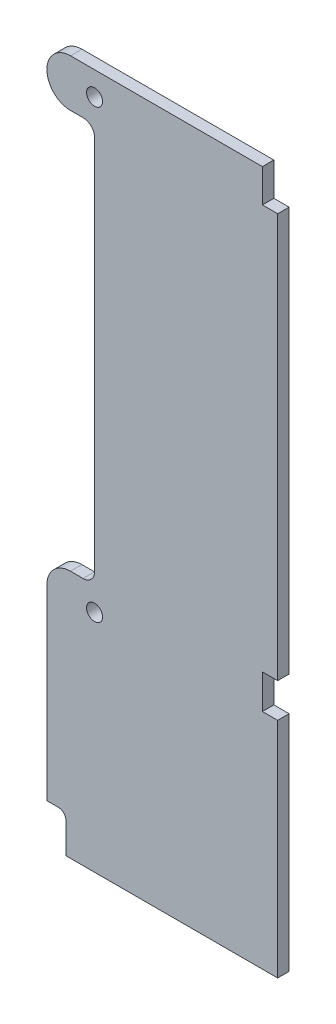
SolidWorks part; units mm, degrees
material "6061-T6 Black anodised"
ref_plane "Front Plane" through (0, 0, 0) normal (0, 0, 1) x (1, 0, 0)
ref_plane "Top Plane" through (0, 0, 0) normal (0, 1, 0) x (1, 0, 0)
ref_plane "Right Plane" through (0, 0, 0) normal (1, 0, 0) x (0, 0, -1)
sketch "Sketch1" plane through (0, 0, 0) normal (0, 0, 1) x (1, 0, 0)
  line L0 (-6.3, 110.8) -> (-3, 110.8)
  line L1 (-6.3, 123.2) -> (44, 123.2)
  line L2 (-12.5, 0) -> (-12.5, -49)
  line L3 (-7.5, -59) -> (48, -59)
  line L4 (-12.5, -49) -> (-9.5, -49)
  line L5 (0, 107.8) -> (0, 9.2)
  line L6 (-3, 6.2) -> (-6.3, 6.2)
  line L7 (48, -0.5) -> (44, -0.5)
  line L8 (44, -0.5) -> (44, 8.5)
  line L9 (44, 8.5) -> (48, 8.5)
  line L10 (48, 114.5) -> (44, 114.5)
  line L11 (44, 114.5) -> (44, 123.2)
  line L12 (-7.5, -51) -> (-7.5, -59)
  line L13 (48, 114.5) -> (48, 8.5)
  line L14 (48, -0.5) -> (48, -59)
  circle A0 centre (0, 0) radius 2.1
  circle A1 centre (0, 117) radius 2.1
  arc A2 (-7.5, -51) -> (-9.5, -49) centre (-9.5, -51) ccw
  arc A3 (-6.3, 6.2) -> (-12.5, 0) centre (-6.3, 0) ccw
  arc A4 (0, 107.8) -> (-3, 110.8) centre (-3, 107.8) ccw
  arc A5 (0, 9.2) -> (-3, 6.2) centre (-3, 9.2) cw
  arc A6 (-6.3, 123.2) -> (-6.3, 110.8) centre (-6.3, 117) ccw
  point P10 (-12.5, 117)
  point P27 (44, 4)
  dimension "D6" = 4.2
  dimension "D8" = 3
  dimension "D15" = 2
  dimension "D1" = 12.5
  dimension "D2" = 117
  dimension "D3" = 59
  dimension "D4" = 182.2
  dimension "D5" = 114.5
  dimension "D7" = 12.5
  dimension "D9" = 9
  dimension "D10" = 4
  dimension "D11" = 48
  dimension "D12" = 4
  dimension "D13" = 5
  dimension "D14" = 10
extrude "Boss-Extrude1" add sketch "Sketch1" along normal blind 3
